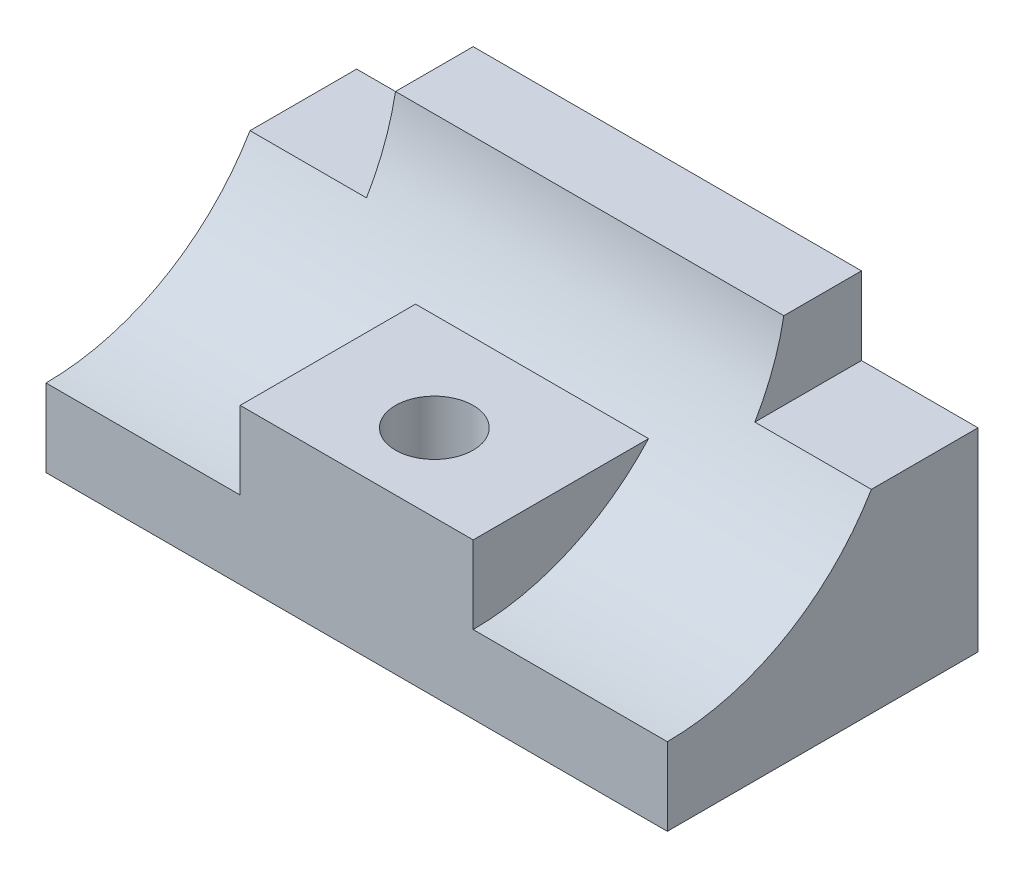
SolidWorks part; units mm, degrees
ref_plane "Alzado" through (0, 0, 0) normal (0, 0, 1) x (1, 0, 0)
ref_plane "Planta" through (0, 0, 0) normal (0, 1, 0) x (1, 0, 0)
ref_plane "Vista lateral" through (0, 0, 0) normal (1, 0, 0) x (0, 0, -1)
sketch "Croquis1" plane through (0, 0, 0) normal (1, 0, 0) x (0, 0, -1)
  line L0 (0, 0) -> (0, 70)
  line L1 (0, 70) -> (-20, 70)
  line L2 (-80, 20) -> (-80, 0)
  line L3 (-80, 0) -> (0, 0)
  arc A0 (-20, 70) -> (-80, 20) centre (-80, 81) cw
  point P6 (-80, 16.636)
  dimension "D5" = 61
  dimension "D1" = 70
  dimension "D2" = 20
  dimension "D3" = 20
extrude "Saliente-Extruir1" add sketch "Croquis1" along normal mid plane 160
sketch "Croquis2" plane through (0, 0, 0) normal (0, 0, 1) x (1, 0, 0)
  line L0 (0, 70) -> (0, -21.6508) construction
  line L1 (-80, 70) -> (-50, 70)
  line L2 (-80, 70) -> (-80, 50)
  line L3 (-80, 50) -> (-50, 50)
  line L4 (-50, 70) -> (-50, 50)
  line L5 (80, 70) -> (-80, 70) construction
  line L6 (50, 70) -> (50, 50)
  line L7 (80, 50) -> (50, 50)
  line L8 (80, 70) -> (80, 50)
  line L9 (80, 70) -> (50, 70)
  dimension "D1" = 30
  dimension "D2" = 20
extrude "Cortar-Extruir1" cut sketch "Croquis2" along normal through all and the other way through all
sketch "Croquis3" plane through (0, 0, 0) normal (0, 0, 1) x (1, 0, 0)
  line L5 (80, 0) -> (-80, 0) construction
  line L6 (-30, 0) -> (30, 0)
  line L7 (-30, 0) -> (-30, 40)
  line L8 (-30, 40) -> (30, 40)
  line L9 (30, 0) -> (30, 40)
  point P6 (0, 0)
  dimension "D1" = 40
  dimension "D2" = 60
extrude "Saliente-Extruir2" add sketch "Croquis3" along normal up to vertex (80 mm away) up to point (80, 0, 80)
sketch "Croquis4" plane through (0, 0, 0) normal (0, 1, 0) x (1, 0, 0)
  line L0 (30, -80) -> (-30, -80) construction
  circle A0 centre (0, -60) radius 10
  point P2 (0, 0)
  point P3 (0, 0)
  point P6 (0, 0)
  point P7 (0, -80)
  dimension "D1" = 20
  dimension "D2" = 20
extrude "Cortar-Extruir2" cut sketch "Croquis4" along normal up to vertex (40 mm away) up to point (30, 40, 80)
